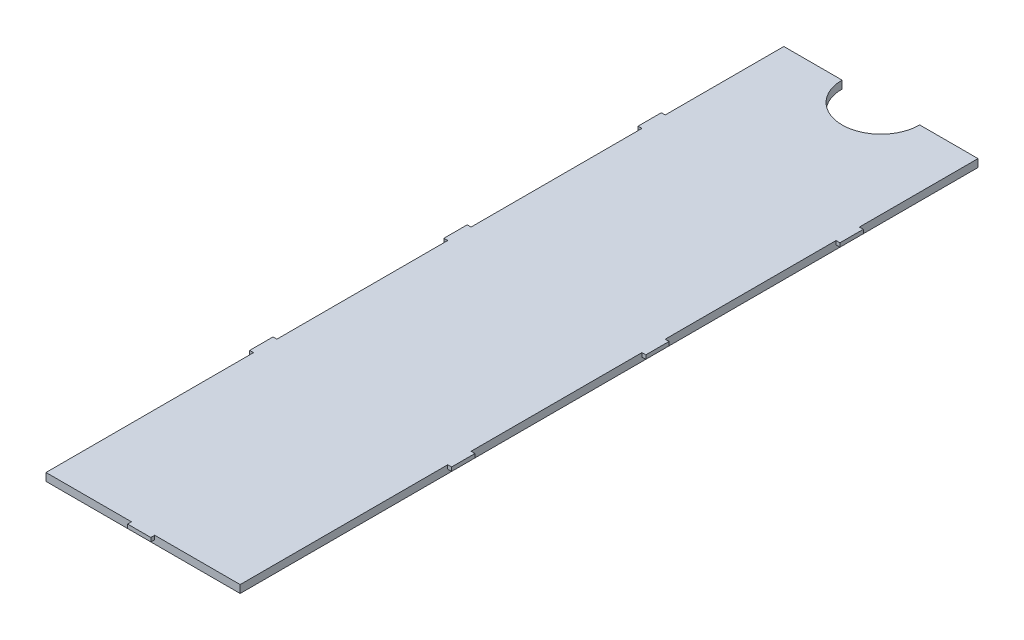
SolidWorks part; units mm, degrees
ref_plane "Front Plane" through (0, 0, 0) normal (0, 0, 1) x (1, 0, 0)
ref_plane "Top Plane" through (0, 0, 0) normal (0, 1, 0) x (1, 0, 0)
ref_plane "Right Plane" through (0, 0, 0) normal (1, 0, 0) x (0, 0, -1)
sketch "Sketch1" plane through (0, 34.2741, 0) normal (0, -1, 0) x (1, 0, 0)
  line L1 (-69.1013, 1.8075) -> (-94.1013, 1.8075)
  line L2 (-69.1013, 1.8075) -> (-69.1013, 96.8075)
  line L3 (-69.1013, 96.8075) -> (-94.1013, 96.8075)
  line L4 (-94.1013, 1.8075) -> (-94.1013, 96.8075)
  line L12 (-79.7254, 94.2365) -> (-81.4772, 95.3785) construction
  line L13 (-81.4772, 94.2365) -> (-79.7254, 95.3785) construction
  line L14 (-94.1013, 1.8075) -> (-94.1013, 49.3075) construction
  line L15 (-94.1013, 49.3075) -> (-94.1013, 96.8075) construction
  point P13 (-80.6013, 94.8075)
extrude "Boss-Extrude1" add sketch "Sketch1" against normal blind 1
sketch "Sketch3" plane through (0, 34.2741, 0) normal (0, -1, 0) x (1, 0, 0)
  line L0 (-69.1013, 96.8075) -> (-94.1013, 96.8075) construction
  line L1 (-80.1013, 96.3075) -> (-83.1013, 96.3075)
  line L2 (-80.1013, 96.3075) -> (-80.1013, 97.3075)
  line L3 (-83.1013, 96.3075) -> (-83.1013, 97.3075)
  line L4 (-80.1013, 97.3075) -> (-83.1013, 97.3075)
  line L5 (-80.1013, 96.3075) -> (-83.1013, 97.3075) construction
  line L6 (-83.1013, 96.3075) -> (-80.1013, 97.3075) construction
  line L7 (-94.6013, 67.0803) -> (-94.6013, 70.0803)
  line L8 (-94.1013, 1.8075) -> (-94.1013, 96.8075) construction
  line L9 (-94.6013, 42.0803) -> (-94.6013, 45.0803)
  line L10 (-94.6013, 42.0803) -> (-93.6013, 42.0803)
  line L11 (-94.6013, 67.0803) -> (-93.6013, 67.0803)
  line L12 (-94.6013, 70.0803) -> (-93.6013, 70.0803)
  line L13 (-93.6013, 67.0803) -> (-93.6013, 70.0803)
  line L14 (-94.6013, 67.0803) -> (-93.6013, 70.0803) construction
  line L15 (-94.6013, 70.0803) -> (-93.6013, 67.0803) construction
  line L16 (-94.6013, 45.0803) -> (-93.6013, 45.0803)
  line L17 (-93.6013, 42.0803) -> (-93.6013, 45.0803)
  line L18 (-94.6013, 42.0803) -> (-93.6013, 45.0803) construction
  line L19 (-94.6013, 45.0803) -> (-93.6013, 42.0803) construction
  line L20 (-94.6013, 17.0803) -> (-94.6013, 20.0803)
  line L21 (-94.6013, 17.0803) -> (-93.6013, 17.0803)
  line L22 (-94.6013, 20.0803) -> (-93.6013, 20.0803)
  line L23 (-93.6013, 17.0803) -> (-93.6013, 20.0803)
  line L24 (-94.6013, 17.0803) -> (-93.6013, 20.0803) construction
  line L25 (-94.6013, 20.0803) -> (-93.6013, 17.0803) construction
  line L27 (-81.6013, 1.8075) -> (-81.6013, 96.8075) construction
  line L28 (-69.1013, 1.8075) -> (-94.1013, 1.8075) construction
  line L29 (-68.6013, 20.0803) -> (-69.6013, 17.0803) construction
  line L30 (-68.6013, 17.0803) -> (-69.6013, 20.0803) construction
  line L31 (-68.6013, 45.0803) -> (-69.6013, 42.0803) construction
  line L32 (-68.6013, 42.0803) -> (-69.6013, 45.0803) construction
  line L33 (-68.6013, 70.0803) -> (-69.6013, 67.0803) construction
  line L34 (-68.6013, 67.0803) -> (-69.6013, 70.0803) construction
  line L35 (-69.6013, 17.0803) -> (-69.6013, 20.0803)
  line L36 (-68.6013, 20.0803) -> (-69.6013, 20.0803)
  line L37 (-68.6013, 17.0803) -> (-69.6013, 17.0803)
  line L38 (-68.6013, 17.0803) -> (-68.6013, 20.0803)
  line L39 (-69.6013, 42.0803) -> (-69.6013, 45.0803)
  line L40 (-68.6013, 45.0803) -> (-69.6013, 45.0803)
  line L41 (-69.6013, 67.0803) -> (-69.6013, 70.0803)
  line L42 (-68.6013, 70.0803) -> (-69.6013, 70.0803)
  line L43 (-68.6013, 67.0803) -> (-69.6013, 67.0803)
  line L44 (-68.6013, 42.0803) -> (-69.6013, 42.0803)
  line L45 (-68.6013, 42.0803) -> (-68.6013, 45.0803)
  line L46 (-68.6013, 67.0803) -> (-68.6013, 70.0803)
  point P0 (-81.6013, 96.8075)
  point P4 (-81.6013, 96.8075)
  point P6 (-93.1057, 46.5719)
  point P11 (-93.1057, 46.5719)
  point P12 (-94.1013, 43.5803)
  point P14 (-93.1057, 25.0719)
  point P15 (-93.1057, 71.5719)
  point P16 (-94.1013, 43.5803)
  point P18 (-93.1057, 71.5719)
  point P19 (-94.1013, 68.5803)
  point P20 (-94.1013, 68.5803)
  point P29 (-93.1057, 21.5719)
  point P30 (-93.1057, 21.5719)
  point P31 (-94.1013, 18.5803)
  point P32 (-94.1013, 18.5803)
  point P51 (-69.1013, 18.5803)
  point P52 (-70.0968, 21.5719)
  point P53 (-69.1013, 68.5803)
  point P54 (-70.0968, 71.5719)
  point P55 (-69.1013, 43.5803)
  point P56 (-70.0968, 25.0719)
  point P57 (-70.0968, 46.5719)
  dimension "D1" = 3
  dimension "D2" = 0
  dimension "D3" = 0.5
  dimension "D4" = 3
  dimension "D5" = 0.5
  dimension "D6" = 3
extrude "Boss-Extrude2" add sketch "Sketch3" against normal blind 0.5 from offset 0.5 offset against normal yes
sketch "Sketch4" plane through (0, 34.2741, 0) normal (0, -1, 0) x (1, 0, 0)
  line L1 (-69.1013, 1.8075) -> (-94.1013, 1.8075) construction
  circle A0 centre (-81.6013, 1.8075) radius 5
  dimension "D1" = 10
extrude "Cut-Extrude1" cut sketch "Sketch4" against normal blind 1
